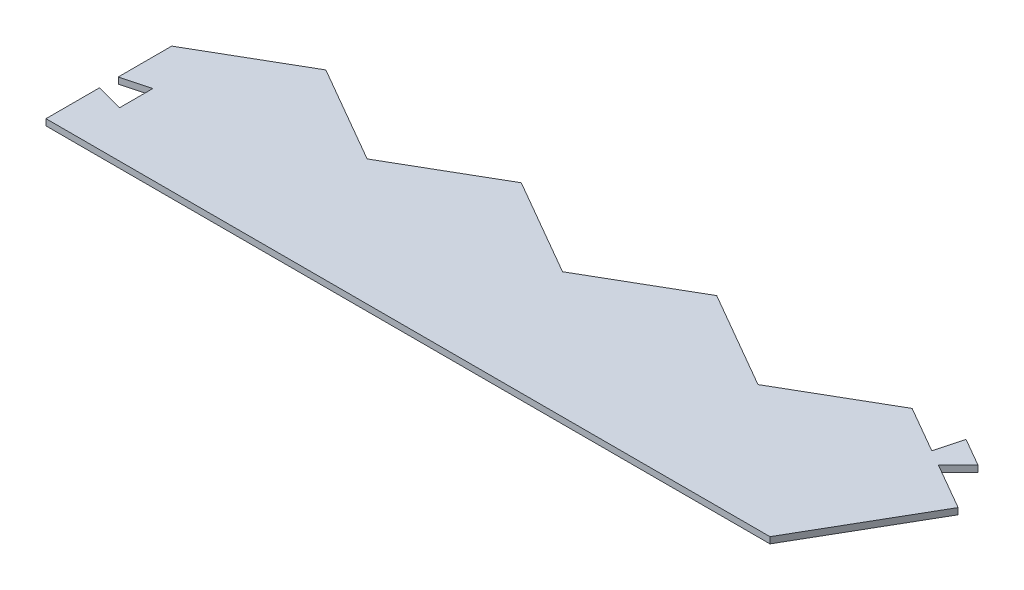
SolidWorks part; units mm, degrees
ref_plane "Front Plane" through (0, 0, 0) normal (0, 0, 1) x (1, 0, 0)
ref_plane "Top Plane" through (0, 0, 0) normal (0, 1, 0) x (1, 0, 0)
ref_plane "Right Plane" through (0, 0, 0) normal (1, 0, 0) x (0, 0, -1)
sketch "Sketch1" plane through (0, 0, 0) normal (0, 1, 0) x (1, 0, 0)
  line L0 (0, 0) -> (0, 21.59)
  line L1 (0, 50.8) -> (39.4847, 73.5965)
  line L2 (39.4847, 73.5965) -> (78.9694, 50.8)
  line L4 (78.9694, 0) -> (0, 0)
  line L6 (78.9694, 50.8) -> (118.4541, 73.5965)
  line L7 (118.4541, 73.5965) -> (157.9388, 50.8)
  line L9 (156.619, 0) -> (78.9694, 0)
  line L11 (157.9388, 50.8) -> (197.4235, 73.5965)
  line L12 (197.4235, 73.5965) -> (236.9082, 50.8)
  line L13 (234.9284, 0) -> (156.619, 0)
  line L14 (236.9082, 50.8) -> (276.3929, 73.5965)
  line L15 (276.3929, 73.5965) -> (295.2003, 62.738)
  line L18 (320.387, 48.1965) -> (292.5607, 0)
  line L19 (292.5607, 0) -> (234.9284, 0)
  line L20 (295.2003, 62.738) -> (298.1258, 73.6559)
  line L21 (298.1258, 73.6559) -> (309.5719, 67.0474)
  line L22 (309.5719, 67.0474) -> (301.5795, 59.055)
  line L23 (0, 29.21) -> (11.0405, 32.1683)
  line L24 (11.0405, 32.1683) -> (11.0405, 18.6317)
  line L25 (11.0405, 18.6317) -> (0, 21.59)
  line L26 (301.5795, 59.055) -> (320.387, 48.1965)
  line L27 (0, 29.21) -> (0, 50.8)
  dimension "D1" = 50.8
  dimension "D2" = 30
  dimension "D3" = 120
  dimension "D4" = 45.593
  dimension "D5" = 50.8
  dimension "D6" = 120
  dimension "D7" = 120
  dimension "D8" = 120
  dimension "D9" = 120
  dimension "D10" = 120
  dimension "D11" = 120
  dimension "D12" = 120
  dimension "D13" = 11.43
  dimension "D14" = 21.59
  dimension "D15" = 11.43
  dimension "D16" = 75
  dimension "D17" = 21.59
  dimension "D18" = 75
  dimension "D19" = 75
  dimension "D20" = 11.303
  dimension "D21" = 21.717
  dimension "D22" = 21.717
  dimension "D23" = 50.8
extrude "Boss-Extrude1" add sketch "Sketch1" along normal blind 2.54 contours L19 L13 L9 L4 L0 L25 L24 L23 L27 L1 L2 L6 L7 L11 L12 L14 L15 L20 L21 L22 L26 L18
